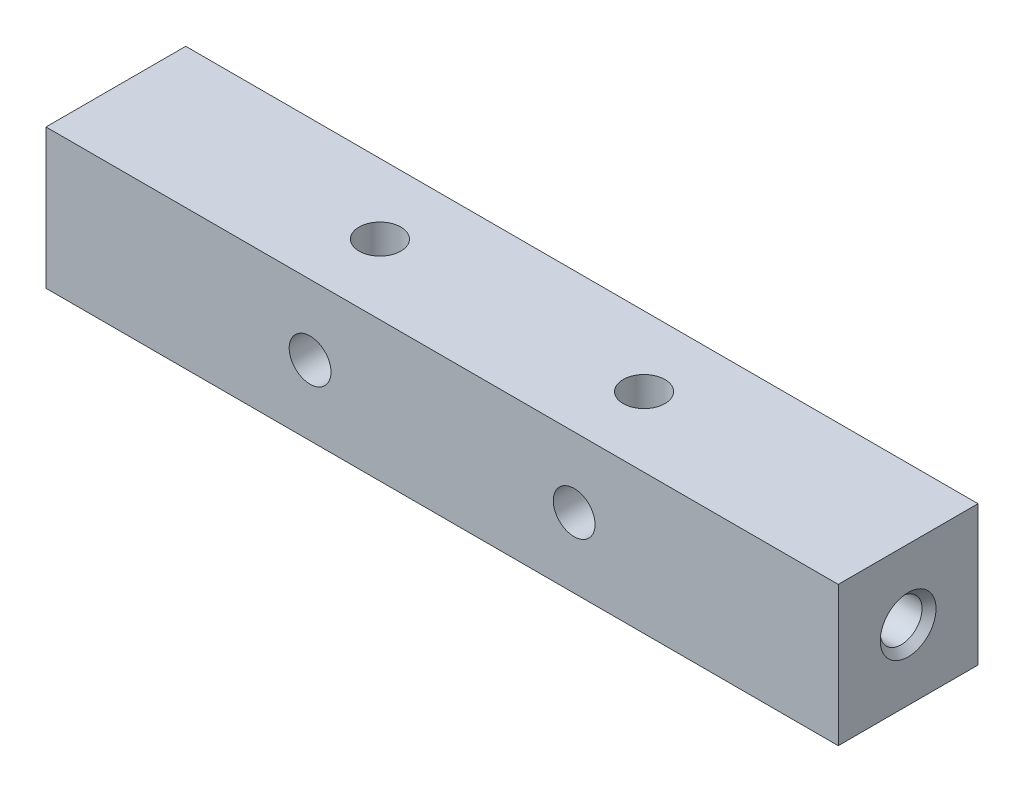
SolidWorks part; units mm, degrees
material "6061 Alloy"
ref_plane "Front Plane" through (0, 0, 0) normal (0, 0, 1) x (1, 0, 0)
ref_plane "Top Plane" through (0, 0, 0) normal (0, 1, 0) x (1, 0, 0)
ref_plane "Right Plane" through (0, 0, 0) normal (1, 0, 0) x (0, 0, -1)
sketch "Sketch1" plane through (0, 0, 0) normal (1, 0, 0) x (0, 0, -1)
  line L1 (6.35, -6.35) -> (-6.35, -6.35)
  line L2 (6.35, -6.35) -> (6.35, 6.35)
  line L3 (6.35, 6.35) -> (-6.35, 6.35)
  line L4 (-6.35, -6.35) -> (-6.35, 6.35)
  line L5 (6.35, -6.35) -> (-6.35, 6.35) construction
  line L6 (6.35, 6.35) -> (-6.35, -6.35) construction
  point P0 (0, 0)
  dimension "D1" = 12.7
  dimension "D2" = 12.7
extrude "Boss-Extrude1" add sketch "Sketch1" along normal blind 72
sketch "Sketch2" plane through (0, 0, 0) normal (-1, 0, 0) x (0, 0, 1)
  circle A0 centre (0, 0) radius 4.7625
  dimension "D1" = 9.525
sketch "Sketch9" plane through (72, 0, 0) normal (1, 0, 0) x (0, 0, -1)
  circle A0 centre (0, 0) radius 4.7625
  dimension "D1" = 9.525
hole_wizard "#10-24 Tapped Hole1" positions "Sketch12" profile "Sketch13" tap size "#10-24" standard "ANSI Inch" end condition through all
sketch "Sketch12" plane through (0, 0, 6.35) normal (0, 0, 1) x (1, 0, 0)
  line L0 (0, 6.35) -> (0, -6.35) construction
  point P0 (24, 0)
  dimension "D1" = 24
sketch "Sketch13" plane through (24, 0, 6.35) normal (1, 0, 0) x (0, -1, 0)
  line L0 (0, 0) -> (0, 12.7)
  line L1 (0, 12.7) -> (1.8986, 12.7)
  line L2 (1.8986, 12.7) -> (1.8986, 0)
  line L5 (1.8986, 0) -> (0, 0)
  line L11 (0, -6.35) -> (0, 107.95) construction
  dimension "Thru Tap Drill Dia." = 3.7973
  dimension "Thru Tap Drill Depth" = 12.7
cosmetic thread "Hole Thread1" parameters "D2"=4.826
hole_wizard "#10-24 Tapped Hole2" positions "Sketch14" profile "Sketch15" tap size "#10-24" standard "ANSI Inch" end condition through all
sketch "Sketch14" plane through (0, 6.35, 0) normal (0, 1, 0) x (1, 0, 0)
  line L0 (0, 6.35) -> (0, -6.35) construction
  point P0 (24, 0)
  dimension "D1" = 24
sketch "Sketch15" plane through (24, 6.35, 0) normal (1, 0, 0) x (0, 0, 1)
  line L0 (0, 0) -> (0, 12.7)
  line L1 (0, 12.7) -> (1.8986, 12.7)
  line L2 (1.8986, 12.7) -> (1.8986, 0)
  line L5 (1.8986, 0) -> (0, 0)
  line L11 (0, -6.35) -> (0, 107.95) construction
  dimension "Thru Tap Drill Dia." = 3.7973
  dimension "Thru Tap Drill Depth" = 12.7
cosmetic thread "Hole Thread2" parameters "D2"=4.826
hole_wizard "M6x1.0 Tapped Hole2" positions "Sketch18" profile "Sketch19" tap size "M6x1.0" standard "ANSI Metric"
sketch "Sketch18" plane through (0, 0, 0) normal (-1, 0, 0) x (0, 0, 1)
  point P0 (0, 0)
sketch "Sketch19" plane through (0, 0, 0) normal (0, 1, 0) x (0, 0, 1)
  line L0 (0, 0) -> (0, 21.8222)
  line L1 (0, 21.8222) -> (2.5, 20.32)
  line L2 (2.5, 20.32) -> (2.5, 0.525)
  line L3 (2.5, 0.525) -> (3.025, 0)
  line L5 (3.025, 0) -> (0, 0)
  line L6 (-2.5, 0.525) -> (-3.025, 0) construction
  line L10 (0, 21.8222) -> (-2.5, 20.32) construction
  line L11 (0, -6.35) -> (0, 107.95) construction
  dimension "Tap Drill Dia." = 5
  dimension "Tap Drill Depth" = 20.32
  dimension "Near C'Sink Dia." = 6.05
  dimension "Near C'Sink Angle" = 90
  dimension "Drill Angle" = 118
cosmetic thread "Hole Thread6" parameters "D1"=15.24, "D2"=6
hole_wizard "#10-24 Tapped Hole3" positions "Sketch20" profile "Sketch21" tap size "#10-24" standard "ANSI Inch"
sketch "Sketch20" plane through (72, 0, 0) normal (1, 0, 0) x (0, 0, -1)
  point P0 (0, 0)
sketch "Sketch21" plane through (72, 0, 0) normal (0, 1, 0) x (0, 0, -1)
  line L0 (0, 0) -> (0, 21.7148)
  line L1 (0, 21.7148) -> (1.8986, 20.574)
  line L2 (1.8986, 20.574) -> (1.8986, 0.635)
  line L3 (1.8986, 0.635) -> (2.5337, 0)
  line L5 (2.5337, 0) -> (0, 0)
  line L6 (-1.8986, 0.635) -> (-2.5337, 0) construction
  line L10 (0, 21.7148) -> (-1.8987, 20.574) construction
  line L11 (0, -6.35) -> (0, 107.95) construction
  dimension "Tap Drill Dia." = 3.7973
  dimension "Tap Drill Depth" = 20.574
  dimension "Near C'Sink Dia." = 5.0673
  dimension "Near C'Sink Angle" = 90
  dimension "Drill Angle" = 118
cosmetic thread "Hole Thread10" parameters "D1"=15.24, "D2"=6
pattern_linear "LPattern1" count 2 spacing 24 along (1, 0, 0) of "#10-24 Tapped Hole1"
pattern_linear "LPattern2" count 2 spacing 24 along (1, 0, 0) of "#10-24 Tapped Hole2"
